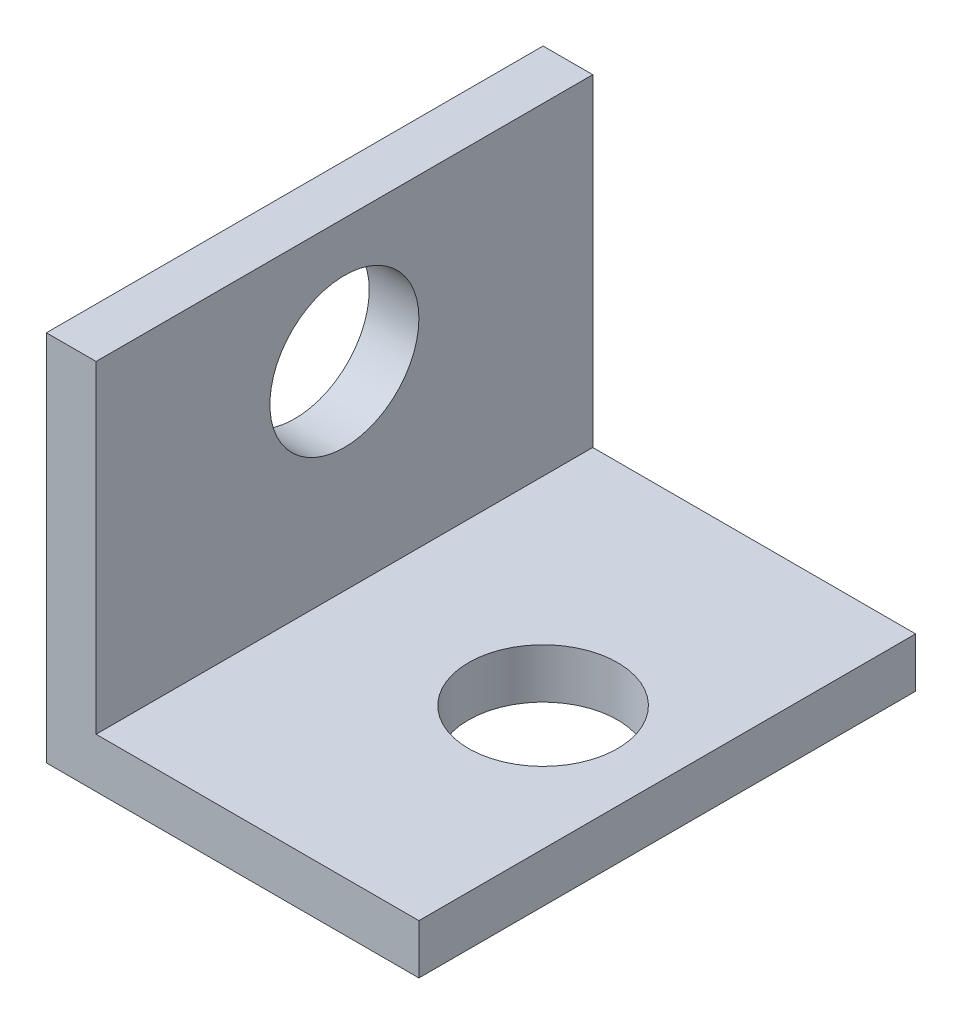
SolidWorks part; units mm, degrees
ref_plane "Front Plane" through (0, 0, 0) normal (0, 0, 1) x (1, 0, 0)
ref_plane "Top Plane" through (0, 0, 0) normal (0, 1, 0) x (1, 0, 0)
ref_plane "Right Plane" through (0, 0, 0) normal (1, 0, 0) x (0, 0, -1)
sketch "Sketch1" plane through (0, 0, 0) normal (0, 0, 1) x (1, 0, 0)
  line L1 (0, 0) -> (15, 0)
  line L2 (15, 0) -> (15, 2)
  line L3 (15, 2) -> (2, 2)
  line L4 (2, 2) -> (2, 15)
  line L5 (2, 15) -> (0, 15)
  line L7 (0, 15) -> (0, 0)
  dimension "D1" = 15
  dimension "D2" = 13
  dimension "D3" = 2
  dimension "D4" = 15
extrude "Boss-Extrude1" add sketch "Sketch1" along normal blind 20
sketch "Sketch2" plane through (0, 2, 0) normal (0, 1, 0) x (1, 0, 0)
  line L0 (0, -20) -> (0, 0) construction
  circle A0 centre (10, -10) radius 3
  dimension "D1" = 6
  dimension "D2" = 10
  dimension "D3" = 10
extrude "Cut-Extrude1" cut sketch "Sketch2" against normal up to next
sketch "Sketch3" plane through (2, 0, 0) normal (1, 0, 0) x (0, 0, -1)
  circle A0 centre (-10, 10) radius 3
  dimension "D1" = 6
  dimension "D2" = 10
  dimension "D3" = 10
extrude "Cut-Extrude2" cut sketch "Sketch3" against normal blind 20
